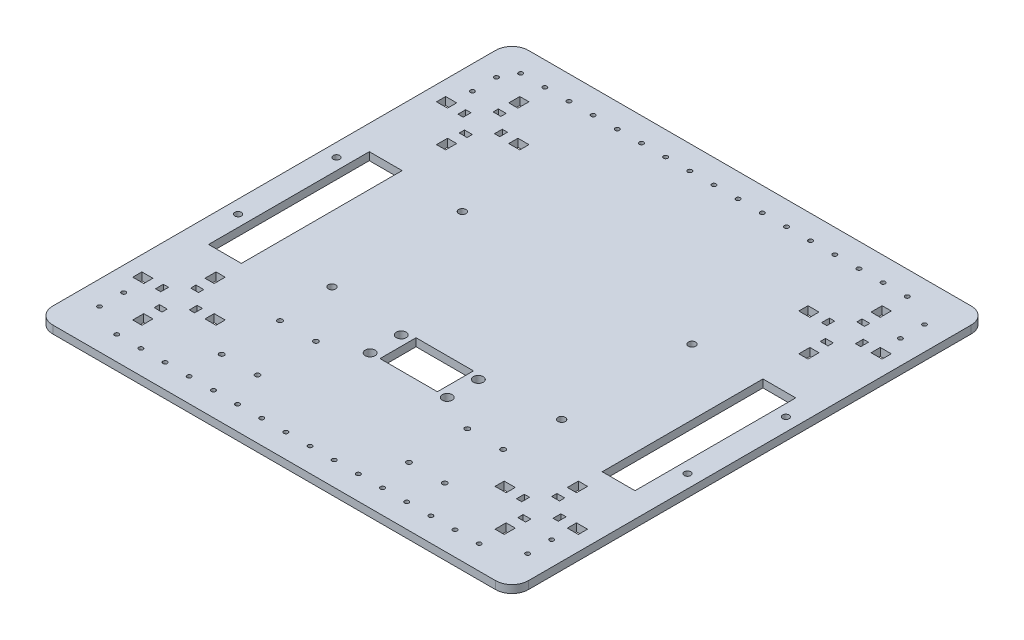
SolidWorks part; units mm, degrees
ref_plane "Front Plane" through (0, 0, 0) normal (0, 0, 1) x (1, 0, 0)
ref_plane "Top Plane" through (0, 0, 0) normal (0, 1, 0) x (1, 0, 0)
ref_plane "Right Plane" through (0, 0, 0) normal (1, 0, 0) x (0, 0, -1)
sketch "Sketch1" plane through (0, 0, 0) normal (0, 1, 0) x (1, 0, 0)
  line L0 (-145, 130.5) -> (145, 130.5) construction
  line L1 (145, -145) -> (-145, -145)
  line L2 (145, -145) -> (145, 145)
  line L3 (145, 145) -> (-145, 145)
  line L4 (-145, -145) -> (-145, 145)
  line L5 (145, -145) -> (-145, 145) construction
  line L6 (145, 145) -> (-145, -145) construction
  line L7 (-145, 116) -> (145, 116) construction
  line L8 (-145, 101.5) -> (145, 101.5) construction
  line L9 (-145, 87) -> (145, 87) construction
  line L10 (-145, 72.5) -> (145, 72.5) construction
  line L11 (-145, 58) -> (145, 58) construction
  line L12 (-145, 43.5) -> (145, 43.5) construction
  line L13 (-145, 29) -> (145, 29) construction
  line L14 (-145, 14.5) -> (145, 14.5) construction
  line L15 (-145, 0) -> (145, 0) construction
  line L16 (-145, -14.5) -> (145, -14.5) construction
  line L17 (-145, -29) -> (145, -29) construction
  line L18 (-145, -43.5) -> (145, -43.5) construction
  line L19 (-145, -58) -> (145, -58) construction
  line L20 (-145, -72.5) -> (145, -72.5) construction
  line L21 (-145, -87) -> (145, -87) construction
  line L22 (-145, -101.5) -> (145, -101.5) construction
  line L23 (-145, -116) -> (145, -116) construction
  line L24 (-145, -130.5) -> (145, -130.5) construction
  line L25 (-145, -145) -> (145, -145) construction
  point P0 (0, 0)
  dimension "D1" = 290
  dimension "D2" = 290
  dimension "D3" = 14.5
  dimension "D5" = 14.5
  dimension "D4" = 20
extrude "Base Plate" add sketch "Sketch1" along normal blind 4.7625
hole_wizard "Caster Holes" positions "Sketch2" profile "Sketch3" hole size "M2" standard "ANSI Metric" end condition through all
sketch "Sketch2" plane through (0, 4.7625, 0) normal (0, 1, 0) x (1, 0, 0)
  line L5 (0, -145) -> (0, 145) construction
  line L6 (145, 145) -> (-145, 145) construction
  line L8 (-145, 0) -> (145, 0) construction
  line L9 (-145, 0) -> (145, 0) construction
  line L10 (-145, 130.5) -> (145, 130.5) construction
  point P200 (-7.366, 130.5)
  point P217 (-22.098, 130.5)
  point P218 (-36.83, 130.5)
  point P219 (-51.562, 130.5)
  point P220 (-66.294, 130.5)
  point P221 (-81.026, 130.5)
  point P222 (-95.758, 130.5)
  point P223 (-110.49, 130.5)
  point P224 (110.49, 130.5)
  point P225 (95.758, 130.5)
  point P226 (81.026, 130.5)
  point P227 (66.294, 130.5)
  point P228 (51.562, 130.5)
  point P229 (36.83, 130.5)
  point P230 (22.098, 130.5)
  point P231 (7.366, 130.5)
  point P232 (7.366, -130.5)
  point P233 (22.098, -130.5)
  point P234 (36.83, -130.5)
  point P235 (51.562, -130.5)
  point P236 (66.294, -130.5)
  point P237 (81.026, -130.5)
  point P238 (95.758, -130.5)
  point P239 (110.49, -130.5)
  point P240 (-110.49, -130.5)
  point P241 (-95.758, -130.5)
  point P242 (-81.026, -130.5)
  point P243 (-66.294, -130.5)
  point P244 (-51.562, -130.5)
  point P245 (-36.83, -130.5)
  point P246 (-22.098, -130.5)
  point P247 (-7.366, -130.5)
  point P250 (-125.222, 130.5)
  dimension "D1" = 7.366
  dimension "D3" = 14.732
  dimension "D2" = 9
sketch "Sketch3" plane through (-125.222, 4.7625, -130.5) normal (1, 0, 0) x (0, 0, 1)
  line L0 (0, 0) -> (0, 4.7625)
  line L1 (0, 4.7625) -> (1.3, 4.7625)
  line L2 (1.3, 4.7625) -> (1.3, 0)
  line L5 (1.3, 0) -> (0, 0)
  line L11 (0, -6.35) -> (0, 107.95) construction
  dimension "Thru Hole Dia." = 2.6
  dimension "Thru Hole Depth" = 4.7625
fillet "Fillet1" radius 10 4 edges at (145, 2.3813, 145) (-145, 2.3813, 145) (145, 2.3813, -145) (-145, 2.3813, -145)
sketch "Sketch4" plane through (0, 0, 0) normal (0, -1, 0) x (1, 0, 0)
  line L0 (145, 0) -> (-145, 0) construction
  line L1 (-145, -135) -> (-145, 135) construction
  line L2 (0, -145) -> (0, 145) construction
  line L3 (-135, 145) -> (135, 145) construction
  point P6 (0, 0)
  point P12 (0, 0)
sketch "Sketch5" plane through (0, 4.7625, 0) normal (0, 1, 0) x (1, 0, 0)
  line L0 (0, 145) -> (0, -145) construction
  line L1 (145, 0) -> (-145, 0) construction
  line L2 (0, 145) -> (0, -145) construction
  line L3 (-17.5, -63) -> (-17.5, -41)
  line L4 (-17.5, -13) -> (17.5, -13) construction
  line L5 (-17.5, -13) -> (-17.5, 9) construction
  line L6 (-17.5, 9) -> (17.5, 9) construction
  line L7 (17.5, -13) -> (17.5, 9) construction
  line L8 (-17.5, -13) -> (17.5, 9) construction
  line L9 (-17.5, 9) -> (17.5, -13) construction
  line L10 (-17.5, -63) -> (17.5, -63)
  line L11 (17.5, -63) -> (17.5, -41)
  line L12 (-17.5, -41) -> (17.5, -41)
  circle A0 centre (-23.5, 6) radius 3 construction
  circle A2 centre (-23.5, -13) radius 3 construction
  circle A3 centre (23.5, 6) radius 3 construction
  circle A4 centre (23.5, -13) radius 3 construction
  circle A5 centre (-23.5, -44) radius 3
  circle A6 centre (-23.5, -63) radius 3
  circle A7 centre (23.5, -63) radius 3
  circle A8 centre (23.5, -44) radius 3
  point P2 (0, -41)
  point P13 (0, -2)
  dimension "D1" = 6
  dimension "D2" = 23.5
  dimension "D3" = 6
  dimension "D4" = 19
  dimension "D5" = 6
  dimension "D6" = 6
  dimension "D8" = 28
  dimension "D7" = 2
extrude "Reflect Holes" cut sketch "Sketch5" against normal up to surface (4.7625 mm away) up to face at (-7.366, 0, -129.2)
sketch "Sketch6" plane through (0, 4.7625, 0) normal (0, 1, 0) x (1, 0, 0)
  line L0 (-137, 145) -> (-137, -145) construction
  line L1 (135, 145) -> (-135, 145) construction
  line L2 (-135, -145) -> (135, -145) construction
  line L3 (-145, 135) -> (-145, -135) construction
  line L16 (145, 0) -> (-145, 0) construction
  line L17 (0, -145) -> (0, 145) construction
  circle A2 centre (-137, 30) radius 2
  circle A22 centre (-137, -30) radius 2
  circle A23 centre (-70, 39.748) radius 2.25
  circle A25 centre (-70, -39.748) radius 2.25
  circle A26 centre (70, -39.748) radius 2.25
  circle A27 centre (70, 39.748) radius 2.25
  circle A28 centre (137, -30) radius 2
  circle A29 centre (137, 30) radius 2
  point P44 (0, 0)
  point P46 (0, 0)
  dimension "D3" = 4
  dimension "D6" = 70
  dimension "D4" = 4.5
  dimension "D1" = 8
  dimension "D2" = 30
  dimension "D5" = 39.748
extrude "bearing slots" cut sketch "Sketch6" against normal up to surface (4.7625 mm away) up to face at (23.5, 0, 47)
sketch "Sketch7" plane through (0, 4.7625, 0) normal (0, 1, 0) x (1, 0, 0)
  line L0 (-145, 135) -> (-145, -135) construction
  line L9 (-130, 43) -> (-110, 43)
  line L10 (-130, 43) -> (-130, -55)
  line L11 (-130, -55) -> (-110, -55)
  line L12 (-110, 43) -> (-110, -55)
  point P9 (-110, -6)
  dimension "D2" = 98
  dimension "D1" = 20
  dimension "D3" = 15
  dimension "D4" = 6
extrude "wheel slots" cut sketch "Sketch7" against normal up to surface (4.7625 mm away) up to face at (-137, 0, 32)
sketch "Sketch9" plane through (0, 4.7625, 0) normal (0, 1, 0) x (1, 0, 0)
  line L0 (-109, -145) -> (-109, 145) construction
  line L1 (135, 145) -> (-135, 145) construction
  line L2 (-145, 135) -> (-145, -135) construction
  line L3 (-135, -145) -> (135, -145) construction
  line L4 (90, -145) -> (90, 145) construction
  line L5 (145, -135) -> (145, 135) construction
  point P0 (-109, -75)
  point P1 (-109, -115)
  point P2 (90, -95)
  point P8 (-109, 0)
  point P21 (90, 0)
  dimension "D1" = 36
  dimension "D2" = 70
  dimension "D3" = 30
  dimension "D4" = 55
  dimension "D5" = 50
sketch "Sketch13" plane through (0, 4.7625, 0) normal (0, 1, 0) x (1, 0, 0)
  line L0 (0, -145) -> (0, 145) construction
  line L7 (135, 145) -> (-135, 145) construction
  line L17 (145, 0) -> (-145, 0) construction
  line L18 (-145, 135) -> (-145, -135) construction
  point P12 (0, 0)
  point P32 (0, 0)
  point P44 (0.04, 0)
mirror "Mirror1" about plane through (0, 0, 0) normal (1, 0, 0) of "wheel slots"
sketch "Sketch15" plane through (0, 4.7625, 0) normal (0, 1, 0) x (1, 0, 0)
  line L21 (-113.25, 118) -> (-107.662, 118)
  line L22 (-113.25, 118) -> (-113.25, 111.269)
  line L23 (-113.25, 111.269) -> (-107.662, 111.269)
  line L24 (-107.662, 118) -> (-107.662, 111.269)
  line L25 (135, 145) -> (-135, 145) construction
  line L26 (-85.056, 95.394) -> (-91.787, 95.394)
  line L27 (-85.056, 95.394) -> (-85.056, 89.806)
  line L28 (-85.056, 89.806) -> (-91.787, 89.806)
  line L29 (-91.787, 95.394) -> (-91.787, 89.806)
  line L30 (-107.662, 67.2) -> (-107.662, 73.931)
  line L31 (-107.662, 67.2) -> (-113.25, 67.2)
  line L32 (-113.25, 67.2) -> (-113.25, 73.931)
  line L33 (-107.662, 73.931) -> (-113.25, 73.931)
  line L34 (-135.856, 89.806) -> (-129.125, 89.806)
  line L35 (-135.856, 89.806) -> (-135.856, 95.394)
  line L36 (-135.856, 95.394) -> (-129.125, 95.394)
  line L37 (-129.125, 89.806) -> (-129.125, 95.394)
  line L38 (-145, 135) -> (-145, -135) construction
  line L39 (-108.4875, 104.925) -> (-113.25, 104.925)
  line L40 (-122.781, 94.5685) -> (-119.581, 94.5685)
  line L41 (-122.781, 94.5685) -> (-122.781, 89.806)
  line L42 (-122.781, 89.806) -> (-119.581, 89.806)
  line L43 (-119.581, 94.5685) -> (-119.581, 89.806)
  line L44 (-108.4875, 104.925) -> (-108.4875, 101.725)
  line L45 (-108.4875, 101.725) -> (-113.25, 101.725)
  line L46 (-113.25, 104.925) -> (-113.25, 101.725)
  line L47 (-98.131, 90.6315) -> (-98.131, 95.394)
  line L48 (-98.131, 90.6315) -> (-101.331, 90.6315)
  line L49 (-101.331, 90.6315) -> (-101.331, 95.394)
  line L50 (-98.131, 95.394) -> (-101.331, 95.394)
  line L51 (-112.4245, 80.275) -> (-107.662, 80.275)
  line L52 (-112.4245, 80.275) -> (-112.4245, 83.475)
  line L53 (-112.4245, 83.475) -> (-107.662, 83.475)
  line L54 (-107.662, 80.275) -> (-107.662, 83.475)
  point P6 (-110.456, 92.6)
  point P10 (-110.456, 111.269)
  point P25 (-110.456, 92.6)
  point P42 (-110.456, 92.6)
  dimension "D1" = 5.588
  dimension "D2" = 6.731
  dimension "D3" = 27
  dimension "D4" = 25.4
  dimension "D6" = 31.75
  dimension "D7" = 3.2
  dimension "D8" = 4.7625
  dimension "D9" = 13.075
  dimension "D5" = 4
  dimension "D10" = 4
extrude "Cut-Extrude2" cut sketch "Sketch15" against normal up to surface (4.7625 mm away) up to face at (-120, 0, 6)
mirror "Mirror2" about plane through (0, 0, 0) normal (1, 0, 0) of "Cut-Extrude2"
mirror "Mirror3" about plane through (0, 0, 0) normal (0, 0, 1) of "Mirror2", "Cut-Extrude2"
sketch "Sketch16" plane through (0, 4.7625, 0) normal (0, 1, 0) x (1, 0, 0)
  line L0 (-135, -145) -> (135, -145) construction
  line L1 (-68, -73.437) -> (-46.16, -73.437) construction
  line L2 (-68, -73.437) -> (-68, -109) construction
  line L3 (-68, -109) -> (-46.16, -109) construction
  line L4 (-46.16, -73.437) -> (-46.16, -109) construction
  line L5 (-145, 135) -> (-145, -135) construction
  line L6 (0, 145) -> (0, -145) construction
  circle A0 centre (-68, -73.437) radius 1.5
  circle A1 centre (-46.16, -73.437) radius 1.5
  circle A2 centre (-46.16, -109) radius 1.5
  circle A3 centre (-68, -109) radius 1.5
  circle A4 centre (46.16, -73.437) radius 1.5
  circle A5 centre (46.16, -109) radius 1.5
  circle A6 centre (68, -109) radius 1.5
  circle A7 centre (68, -73.437) radius 1.5
  point P16 (0, 0)
  dimension "D1" = 3
  dimension "D2" = 21.84
  dimension "D3" = 35.563
  dimension "D4" = 36
  dimension "D5" = 77
extrude "Cut-Extrude3" cut sketch "Sketch16" against normal up to surface (4.7625 mm away) up to face at (-110.0432, 0, 81.875)
sketch "Sketch17" plane through (0, 4.7625, 0) normal (0, 1, 0) x (1, 0, 0)
  line L0 (-145, 135) -> (-145, -135) construction
  line L1 (135, 145) -> (-135, 145) construction
  line L2 (0, -145) -> (0, 145) construction
  line L3 (145, 0) -> (-145, 0) construction
  circle A0 centre (-130.5, 121) radius 1.3
  circle A1 centre (-130.5, 106.3) radius 1.3
  circle A2 centre (-125.222, 130.5) radius 1.3 construction
  circle A3 centre (-130.5, -106.3) radius 1.3
  circle A4 centre (-130.5, -121) radius 1.3
  circle A5 centre (130.5, -121) radius 1.3
  circle A6 centre (130.5, -106.3) radius 1.3
  circle A7 centre (130.5, 106.3) radius 1.3
  circle A8 centre (130.5, 121) radius 1.3
  point P16 (0, 0)
  point P18 (0, 0)
  dimension "D1" = 14.5
  dimension "D2" = 14.7
  dimension "D3" = 24
extrude "Cut-Extrude4" cut sketch "Sketch17" against normal up to surface (4.7625 mm away) up to face at (46.16, 0, 74.937)
